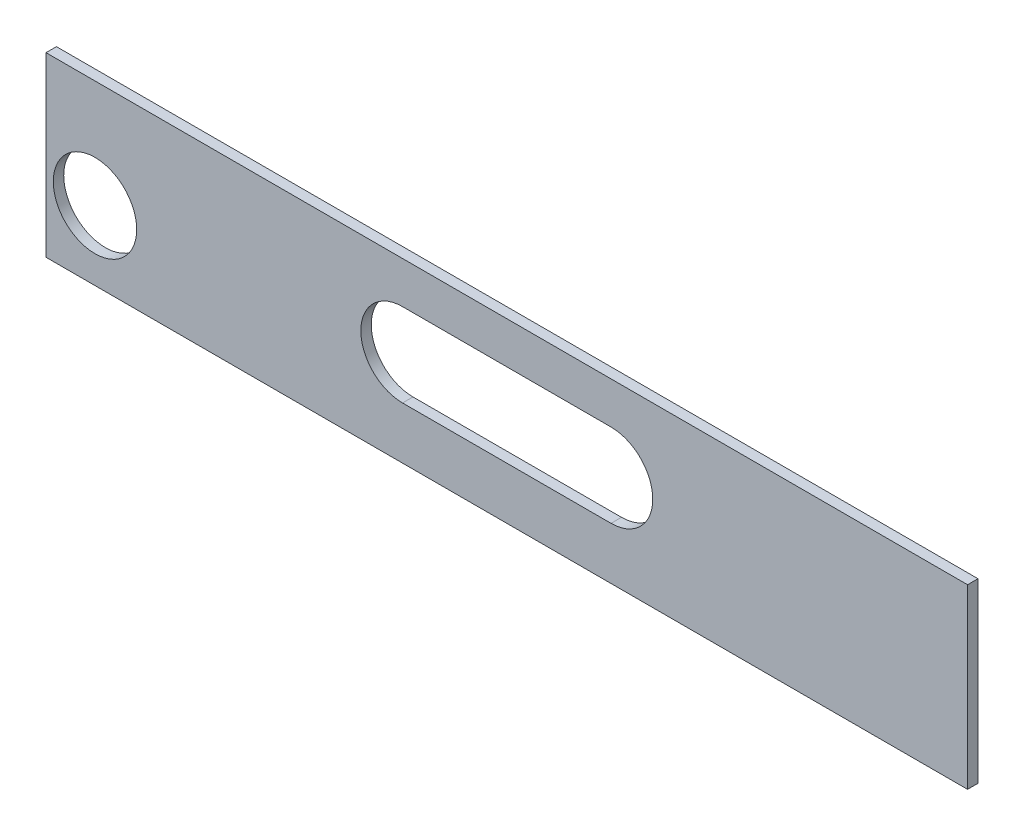
SolidWorks part; units mm, degrees
ref_plane "Front Plane" through (0, 0, 0) normal (0, 0, 1) x (1, 0, 0)
ref_plane "Top Plane" through (0, 0, 0) normal (0, 1, 0) x (1, 0, 0)
ref_plane "Right Plane" through (0, 0, 0) normal (1, 0, 0) x (0, 0, -1)
sketch "Sketch1" plane through (0, 0, 0) normal (0, 0, 1) x (1, 0, 0)
  line L1 (-42.1445, -2.6354) -> (46.2555, -2.6354)
  line L2 (-42.1445, -2.6354) -> (-42.1445, -19.6354)
  line L3 (-42.1445, -19.6354) -> (46.2555, -19.6354)
  line L4 (46.2555, -2.6354) -> (46.2555, -19.6354)
  dimension "D1" = 17
  dimension "D2" = 88.4
extrude "Boss-Extrude1" add sketch "Sketch1" along normal blind 1
sketch "ｽｹｯﾁ1" plane through (0, 0, 0) normal (0, 0, -1) x (-1, 0, 0)
  line L0 (-12.0555, -10.6354) -> (7.9445, -10.6354) construction
  line L1 (-12.0555, -6.6354) -> (7.9445, -6.6354)
  line L2 (-12.0555, -14.6354) -> (7.9445, -14.6354)
  line L3 (-46.2555, -19.6354) -> (-46.2555, -2.6354) construction
  line L4 (42.1445, -2.6354) -> (42.1445, -19.6354) construction
  line L5 (-46.2555, -2.6354) -> (42.1445, -2.6354) construction
  arc A0 (-12.0555, -6.6354) -> (-12.0555, -14.6354) centre (-12.0555, -10.6354) ccw
  arc A1 (7.9445, -14.6354) -> (7.9445, -6.6354) centre (7.9445, -10.6354) ccw
  circle A2 centre (37.4445, -12.9854) radius 4
  point P2 (-2.0555, -10.6354)
  dimension "D1" = 34.2
  dimension "D2" = 34.2
  dimension "D6" = 10.35
  dimension "D7" = 8
  dimension "D5" = 4.7
  dimension "D3" = 4
  dimension "D4" = 8
extrude "ｶｯﾄ - 押し出し1" cut sketch "ｽｹｯﾁ1" against normal blind 10
